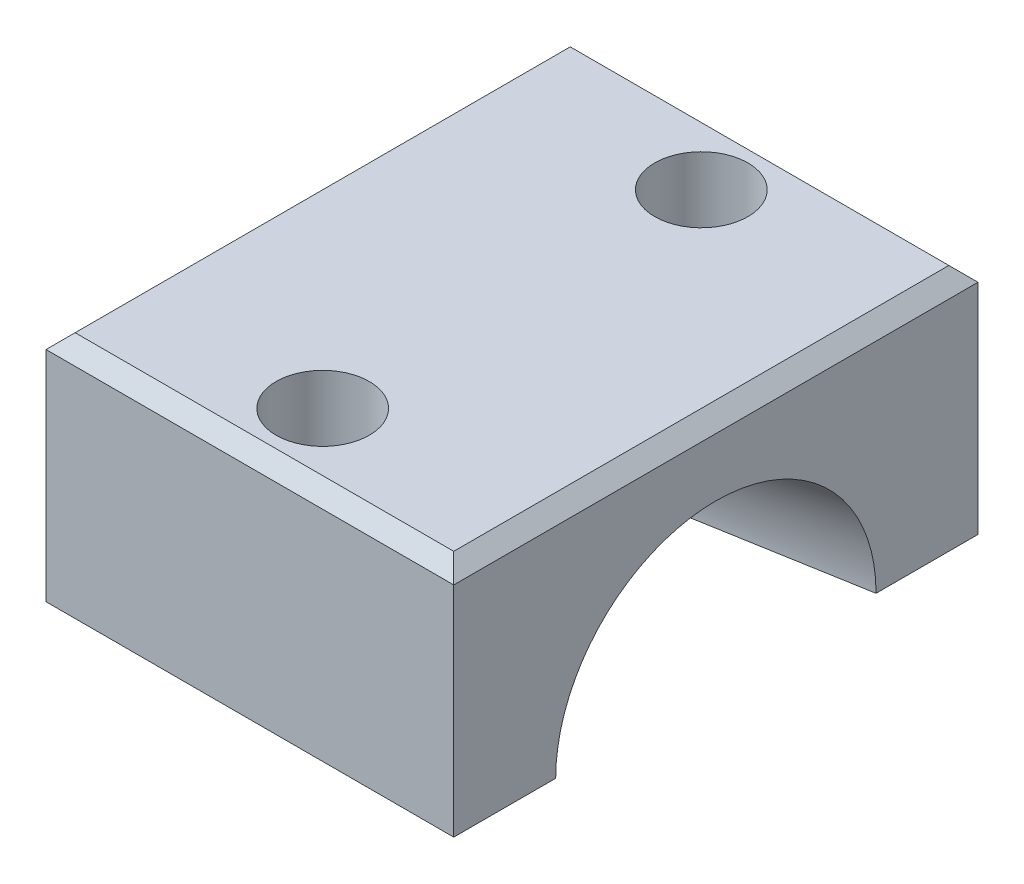
SolidWorks part; units mm, degrees
ref_plane "前基準面" through (0, 0, 0) normal (0, 0, 1) x (1, 0, 0)
ref_plane "上基準面" through (0, 0, 0) normal (0, 1, 0) x (1, 0, 0)
ref_plane "右基準面" through (0, 0, 0) normal (1, 0, 0) x (0, 0, -1)
sketch "草圖1" plane through (0, 0, 0) normal (0, 1, 0) x (1, 0, 0)
  line L0 (-3.5728, 0) -> (5.6377, 0) construction
  line L1 (-7, -9) -> (7, -9)
  line L2 (-7, -9) -> (-7, 9)
  line L3 (-7, 9) -> (7, 9)
  line L4 (7, -9) -> (7, 9)
  line L5 (-7, -9) -> (7, 9) construction
  line L6 (-7, 9) -> (7, -9) construction
  circle A1 centre (0, 6.5) radius 1.6
  circle A2 centre (0, -6.5) radius 1.6
  point P0 (0, 0)
  dimension "D3" = 3.2
  dimension "D4" = 2.5
  dimension "D5" = 7
  dimension "D1" = 18
  dimension "D2" = 14
extrude "填料-伸長1" add sketch "草圖1" along normal mid plane 8
sketch "草圖2" plane through (-7, 0, 0) normal (-1, 0, 0) x (0, 0, 1)
  line L0 (-9, -4) -> (9, -4) construction
  circle A0 centre (0, -4) radius 3.5
  dimension "D1" = 7
extrude "除料-伸長1" cut sketch "草圖2" against normal blind 2.5 contours A0
sketch "草圖3" plane through (-4.5, 0, 0) normal (-1, 0, 0) x (0, 0, 1)
  line L0 (3.5, -4) -> (-3.5, -4) construction
  circle A0 centre (0, -4) radius 3.5
  dimension "D1" = 7
sketch "草圖4" plane through (7, 0, 0) normal (1, 0, 0) x (0, 0, -1)
  circle A0 centre (0, -4) radius 5.5
  dimension "D1" = 11
loft "除料-疊層拉伸1" cut profiles "草圖4", "草圖3"
chamfer "導角1" distance 0.5 angle 45 4 edges at (0, 4, -9) (7, 4, 0) (0, 4, 9) (-7, 4, 0)
